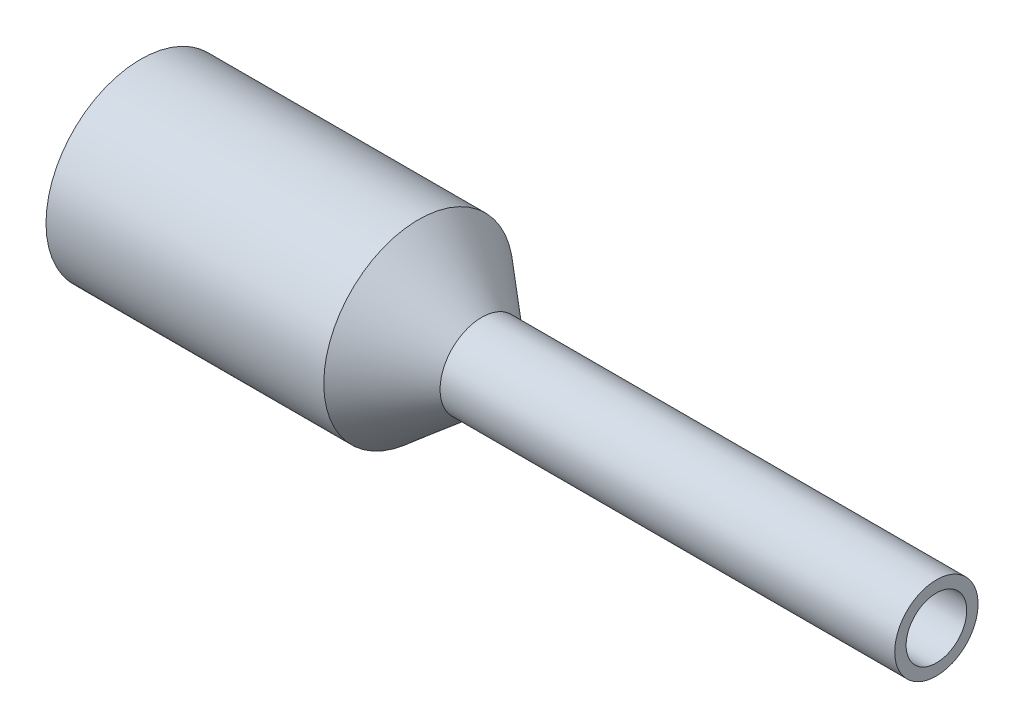
SolidWorks part; units mm, degrees
material "EPDM"
ref_plane "Alzado" through (0, 0, 0) normal (0, 0, 1) x (1, 0, 0)
ref_plane "Planta" through (0, 0, 0) normal (0, 1, 0) x (1, 0, 0)
ref_plane "Vista lateral" through (0, 0, 0) normal (1, 0, 0) x (0, 0, -1)
sketch "Croquis1" plane through (0, 0, 0) normal (0, 0, 1) x (1, 0, 0)
  line L0 (-5.25, 0) -> (5.25, 0) construction
  line L1 (5.25, 0.4) -> (-0.75, 0.4)
  line L2 (5.25, 0.4) -> (5.25, 0) construction
  line L3 (-5.25, 1) -> (-1.4651, 1) construction
  line L4 (-1.4651, 1) -> (-0.75, 0.4) construction
  line L5 (5.25, 0.4) -> (5.25, 0.55)
  line L6 (5.25, 0.55) -> (-0.75, 0.55)
  line L7 (-5.25, 1) -> (-5.25, 1.25)
  line L8 (-5.25, 1.25) -> (-1.5842, 1.25)
  line L9 (-1.5842, 1.25) -> (-0.75, 0.55)
  line L10 (-5.25, 1) -> (-1.5842, 1)
  line L11 (-1.5842, 1) -> (-0.75, 0.4)
  dimension "D1" = 0.8
  dimension "L1" = 10.5
  dimension "L2" = 6
  dimension "D2" = 2
  dimension "D3" = 40
  dimension "D4" = 0.15
  dimension "s2" = 0.25
revolve "Revolución1" add sketch "Croquis1" angle 360 about L0
